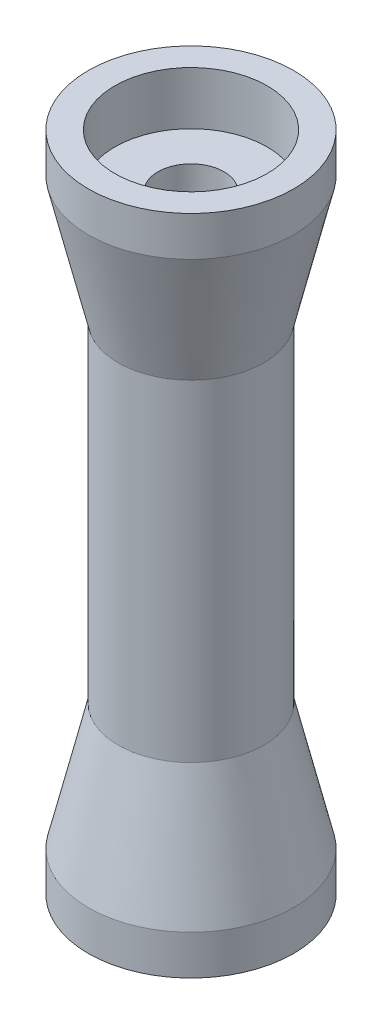
SolidWorks part; units mm, degrees
ref_plane "Plano frontal" through (0, 0, 0) normal (0, 0, 1) x (1, 0, 0)
ref_plane "Plano superior" through (0, 0, 0) normal (0, 1, 0) x (1, 0, 0)
ref_plane "Plano direito" through (0, 0, 0) normal (1, 0, 0) x (0, 0, -1)
sketch "Esboço1" plane through (0, 0, 0) normal (0, 0, 1) x (1, 0, 0)
  line L0 (0, 0) -> (0, 73.2941) construction
  line L1 (11, 25) -> (15.5, 6)
  line L2 (15.5, 6) -> (15.5, 0)
  line L3 (11.5, 92) -> (5, 92)
  line L4 (11, 75) -> (11, 25)
  line L5 (11.5, 100) -> (11.5, 92)
  line L6 (15.5, 0) -> (11.5, 0)
  line L7 (11.5, 0) -> (11.5, 8)
  line L8 (11.5, 8) -> (5, 8)
  line L9 (5, 8) -> (5, 92)
  line L10 (15.5, 100) -> (11.5, 100)
  line L11 (15.5, 94) -> (15.5, 100)
  line L12 (5, 50) -> (63.7516, 50) construction
  line L13 (11, 75) -> (15.5, 94)
  point P17 (11, 50)
  dimension "D1" = 6
  dimension "D2" = 8
  dimension "D3" = 100
  dimension "D4" = 6
  dimension "D5" = 23
  dimension "D6" = 10
  dimension "D7" = 4
  dimension "D8" = 50
revolve "Revolução1" add sketch "Esboço1" angle 360 about L0
